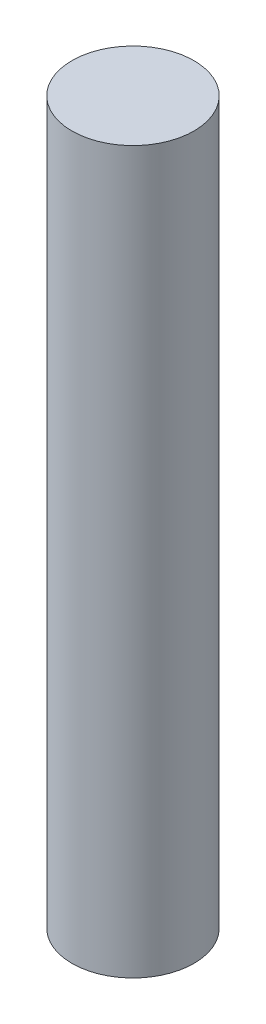
SolidWorks part; units mm, degrees
ref_plane "Front Plane" through (0, 0, 0) normal (0, 0, 1) x (1, 0, 0)
ref_plane "Top Plane" through (0, 0, 0) normal (0, 1, 0) x (1, 0, 0)
ref_plane "Right Plane" through (0, 0, 0) normal (1, 0, 0) x (0, 0, -1)
sketch "Sketch1" plane through (0, 0, 0) normal (0, 1, 0) x (1, 0, 0)
  circle A0 centre (0, 0) radius 1.1
  dimension "D1" = 2.2
extrude "Boss-Extrude1" add sketch "Sketch1" along normal blind 13
